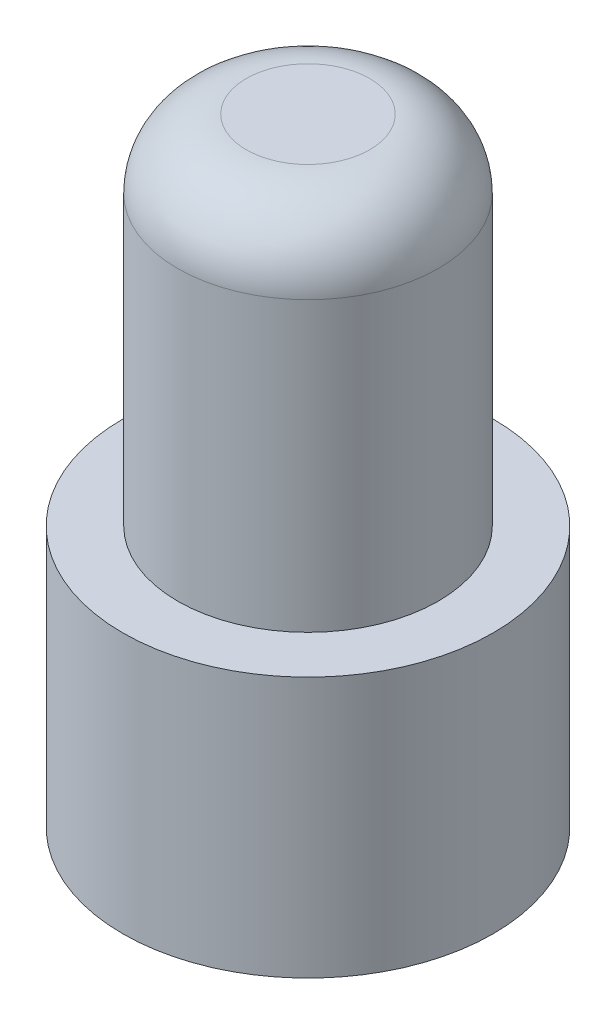
SolidWorks part; units mm, degrees
ref_plane "Plano frontal" through (0, 0, 0) normal (0, 0, 1) x (1, 0, 0)
ref_plane "Plano superior" through (0, 0, 0) normal (0, 1, 0) x (1, 0, 0)
ref_plane "Plano direito" through (0, 0, 0) normal (1, 0, 0) x (0, 0, -1)
sketch "Esboço1" plane through (0, 0, 0) normal (0, 0, 1) x (1, 0, 0)
  line L0 (-13.6191, 0) -> (-13.6191, 9.5)
  line L1 (-13.6191, 9.5) -> (-11.6191, 9.5)
  line L2 (-11.6191, 9.5) -> (-11.6191, 22.5)
  line L3 (-11.6191, 22.5) -> (-6.8691, 22.5)
  line L4 (-6.8691, 8.3829) -> (-6.8691, 19.7693) construction
  line L5 (-13.6191, 0) -> (-6.8691, 0)
  line L10 (-6.8691, 0) -> (-6.8691, 22.5)
  point P6 (-4.84, 0)
  point P11 (0, 0)
  point P14 (-6.6695, 2.5872)
  dimension "D1" = 4.75
  dimension "D2" = 2
  dimension "D3" = 9.5
  dimension "D4" = 13
revolve "Revolução1" add sketch "Esboço1" angle 360 about L10
fillet "Filete1" radius 2.5 1 edges at (-6.8691, 22.5, -4.75)
